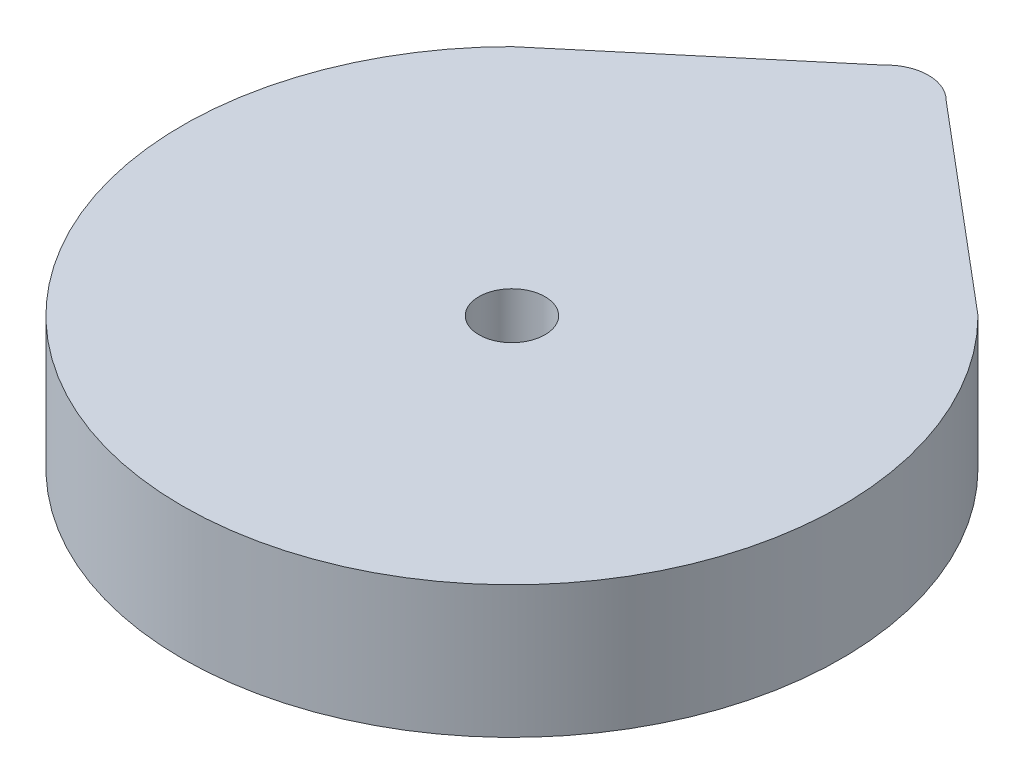
SolidWorks part; units mm, degrees
ref_plane "Front Plane" through (0, 0, 0) normal (0, 0, 1) x (1, 0, 0)
ref_plane "Top Plane" through (0, 0, 0) normal (0, 1, 0) x (1, 0, 0)
ref_plane "Right Plane" through (0, 0, 0) normal (1, 0, 0) x (0, 0, -1)
sketch "Sketch1" plane through (0, 0, 0) normal (0, 1, 0) x (1, 0, 0)
  line L2 (-8.954, 8.954) -> (-1.2083, 15.4727)
  line L5 (8.954, 8.954) -> (1.1735, 15.5096)
  circle A1 centre (0, 0) radius 1.27
  arc A3 (1.1735, 15.5096) -> (-1.2083, 15.4727) centre (0, 14.3662) ccw
  arc A4 (-8.954, 8.954) -> (8.954, 8.954) centre (0, 0) ccw
extrude "Boss-Extrude2" add sketch "Sketch1" along normal blind 5.08 contours A1 | A3 L2 A4 L5
